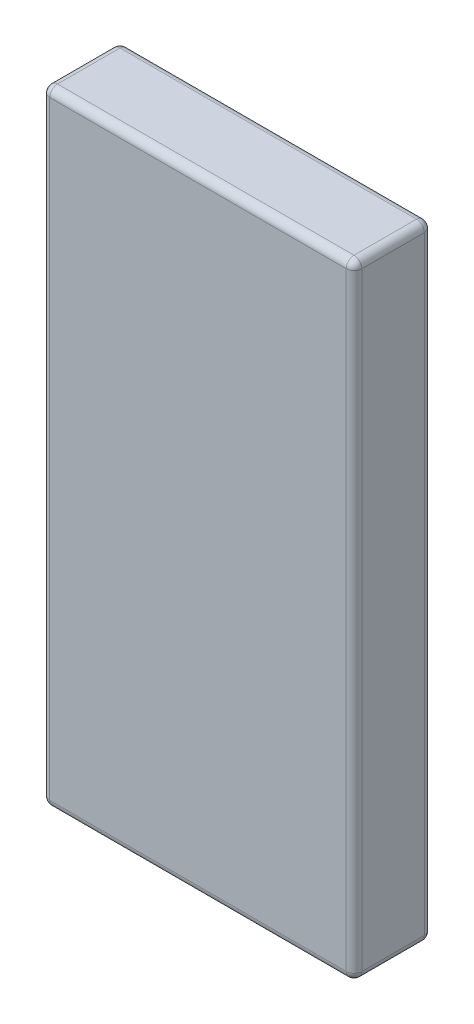
SolidWorks part; units mm, degrees
ref_plane "Front Plane" through (0, 0, 0) normal (0, 0, 1) x (1, 0, 0)
ref_plane "Top Plane" through (0, 0, 0) normal (0, 1, 0) x (1, 0, 0)
ref_plane "Right Plane" through (0, 0, 0) normal (1, 0, 0) x (0, 0, -1)
sketch "Sketch1" plane through (0, 0, 0) normal (0, 0, 1) x (1, 0, 0)
  line L1 (-12.7, 25.4) -> (12.7, 25.4)
  line L2 (-12.7, 25.4) -> (-12.7, -25.4)
  line L3 (-12.7, -25.4) -> (12.7, -25.4)
  line L4 (12.7, 25.4) -> (12.7, -25.4)
  line L5 (-12.7, 25.4) -> (12.7, -25.4) construction
  line L6 (-12.7, -25.4) -> (12.7, 25.4) construction
  point P0 (0, 0)
  dimension "D1" = 50.8
  dimension "D2" = 25.4
extrude "Boss-Extrude1" add sketch "Sketch1" along normal blind 6.35
fillet "Fillet1" radius 0.635 12 edges at (-12.7, -25.4, 3.175) (12.7, -25.4, 3.175) (12.7, 25.4, 3.175) (-12.7, 25.4, 3.175) (0, -25.4, 6.35) (-12.7, 0, 6.35) (0, 25.4, 6.35) (12.7, 0, 6.35) (0, 25.4, 0) (-12.7, 0, 0) (0, -25.4, 0) (12.7, 0, 0)
